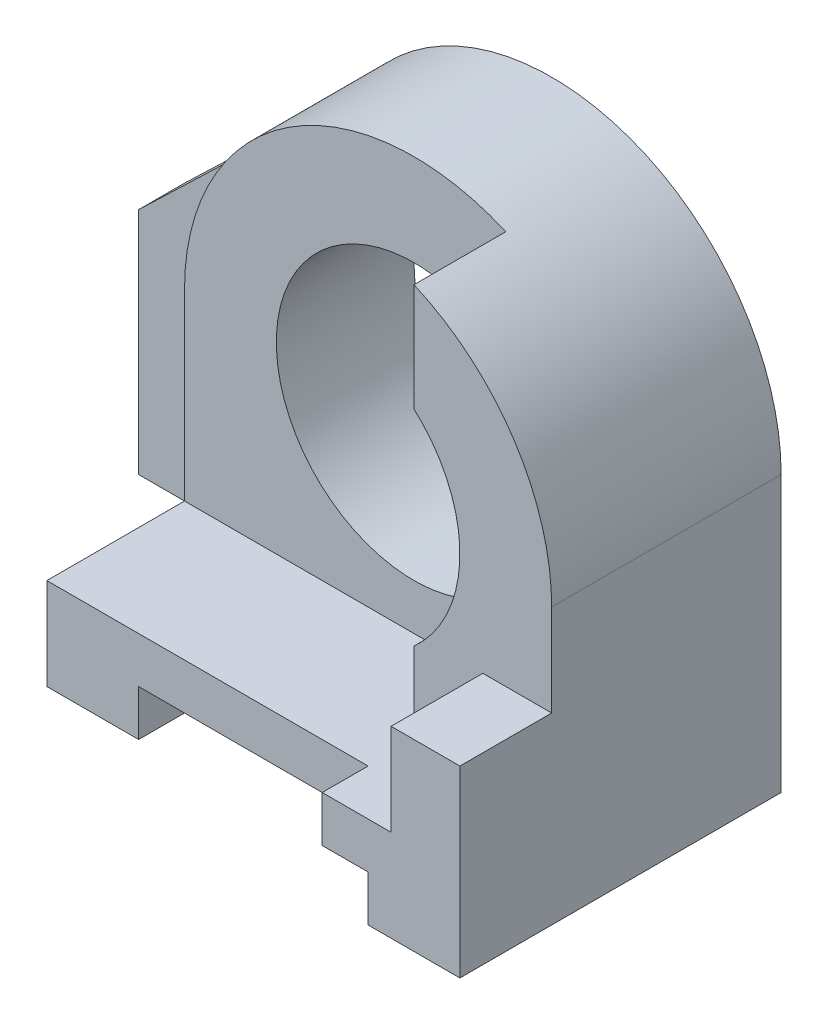
SolidWorks part; units mm, degrees
ref_plane "Front" through (0, 0, 0) normal (0, 0, 1) x (1, 0, 0)
ref_plane "Top" through (0, 0, 0) normal (0, 1, 0) x (1, 0, 0)
ref_plane "Right" through (0, 0, 0) normal (1, 0, 0) x (0, 0, -1)
sketch "Sketch1" plane through (0, 0, 0) normal (0, 0, 1) x (1, 0, 0)
  line L0 (0, 0) -> (2, 0)
  line L1 (2, 0) -> (2, 1)
  line L2 (2, 1) -> (8, 1)
  line L3 (8, 1) -> (8, 0)
  line L4 (8, 0) -> (10, 0)
  line L5 (10, 0) -> (10, 6)
  line L6 (0, 6) -> (0, 0)
  arc A0 (10, 6) -> (0, 6) centre (5, 6) ccw
  circle A1 centre (5, 6) radius 3
  dimension "D6" = 5
  dimension "D8" = 6
  dimension "D1" = 6
  dimension "D2" = 6
  dimension "D3" = 1
  dimension "D4" = 1
  dimension "D5" = 6
  dimension "D7" = 2
extrude "Boss-Extrude1" add sketch "Sketch1" along normal blind 7
sketch "Sketch2" plane through (0, 0, 0) normal (0, 0, -1) x (-1, 0, 0)
  line L0 (0, 0) -> (3, 0)
  line L1 (3, 0) -> (3, 5)
  line L2 (3, 5) -> (-0.7058, 8.5611)
  line L3 (0, 0) -> (-0.312, 0)
  line L4 (0, 0) -> (-2, 0) construction
  line L5 (-0.312, 0) -> (-0.7058, 8.5611)
  arc A0 (0, 6) -> (-10, 6) centre (-5, 6) ccw construction
  dimension "D1" = 3
  dimension "D2" = 5
extrude "Boss-Extrude2" add sketch "Sketch2" against normal blind 1
sketch "Sketch3" plane through (0, 0, 7) normal (0, 0, 1) x (1, 0, 0)
  line L0 (7, 10.5826) -> (7, 2)
  line L1 (7, 2) -> (8.5, 2)
  line L2 (8.5, 2) -> (8.5, 4)
  line L3 (8.5, 4) -> (10, 4)
  line L4 (10, 0) -> (10, 6) construction
  line L5 (10, 4) -> (10, 10.5826)
  line L6 (10, 10.5826) -> (7, 10.5826)
  line L7 (8, 0) -> (10, 0) construction
  arc A0 (10, 6) -> (0, 6) centre (5, 6) ccw construction
  dimension "D1" = 3
  dimension "D2" = 1.5
  dimension "D3" = 2
  dimension "D4" = 2
extrude "Cut-Extrude1" cut sketch "Sketch3" against normal blind 2
sketch "Sketch4" plane through (0, 0, 0) normal (0, 1, 0) x (1, 0, 0)
  line L0 (7, -7) -> (7, -6)
  line L1 (7, -5) -> (7, -7) construction
  line L2 (7, -6) -> (0, -6)
  line L3 (0, -7) -> (0, -1) construction
  line L4 (0, -6) -> (-0.7272, -7.4638)
  line L5 (-0.7272, -7.4638) -> (7.3625, -7.4638)
  line L6 (7.3625, -7.4638) -> (7, -7)
extrude "Cut-Extrude2" cut sketch "Sketch4" along normal blind 12
sketch "Sketch5" plane through (0, 2, 0) normal (0, 1, 0) x (1, 0, 0)
  line L0 (7, -5) -> (7, -3)
  line L1 (7, -3) -> (0, -3)
  line L2 (0, -6) -> (0, -1) construction
  line L3 (0, -3) -> (0, -6)
  line L4 (0, -6) -> (7, -6)
  line L5 (7, -6) -> (7, -5)
  dimension "D1" = 3
extrude "Cut-Extrude3" cut sketch "Sketch5" along normal blind 12
